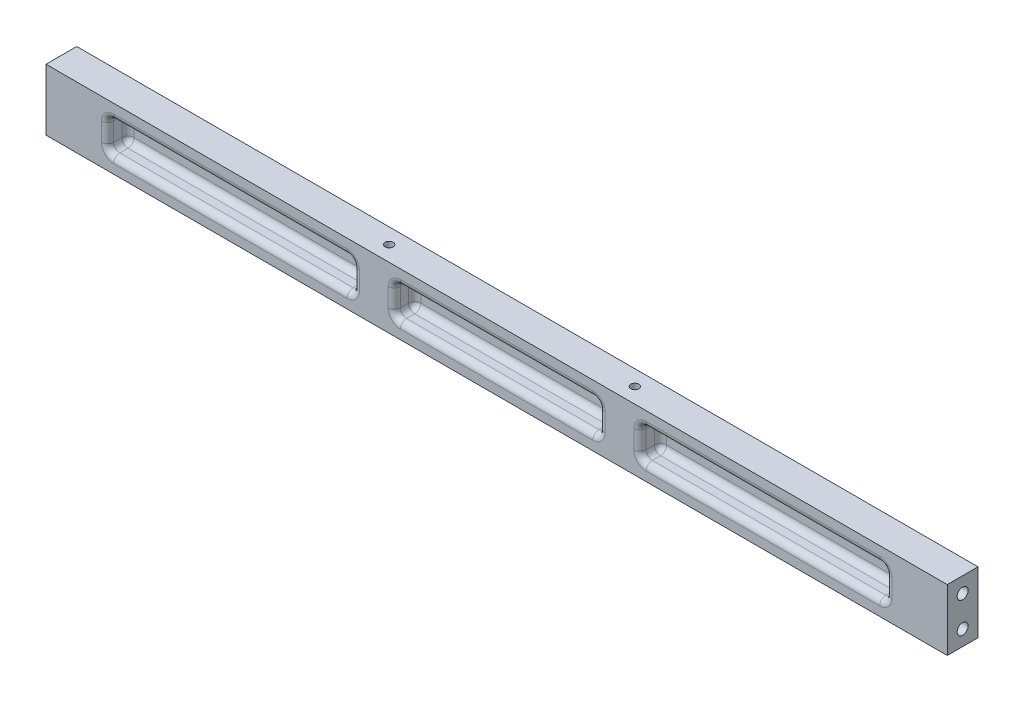
SolidWorks part; units mm, degrees
material "Alum 6061 (Default)"
ref_plane "Front Plane" through (0, 0, 0) normal (0, 0, 1) x (1, 0, 0)
ref_plane "Top Plane" through (0, 0, 0) normal (0, 1, 0) x (1, 0, 0)
ref_plane "Right Plane" through (0, 0, 0) normal (1, 0, 0) x (0, 0, -1)
sketch "Sketch1" plane through (0, 0, 0) normal (0, 0, 1) x (1, 0, 0)
  line L1 (-279.4, 19.05) -> (279.4, 19.05)
  line L2 (-279.4, 19.05) -> (-279.4, -19.05)
  line L3 (-279.4, -19.05) -> (279.4, -19.05)
  line L4 (279.4, 19.05) -> (279.4, -19.05)
  line L5 (-279.4, 19.05) -> (279.4, -19.05) construction
  line L6 (-279.4, -19.05) -> (279.4, 19.05) construction
  point P0 (0, 0)
  dimension "SpreadWidthT" = 558.8
  dimension "Height" = 38.1
extrude "Extrude1" add sketch "Sketch1" along normal mid plane 19.05
hole_wizard "M8x1.25 Tapped Hole1" positions "Sketch6" profile "Sketch7" tap size "M8x1.25" standard "ANSI Metric"
sketch "Sketch6" plane through (-279.4, 0, 0) normal (-1, 0, 0) x (0, 0, 1)
  line L0 (0, 9.525) -> (0, -9.525) construction
  point P0 (0, 9.525)
  point P2 (0, -9.525)
  point P10 (0, 0)
  dimension "D1" = 19.05
sketch "Sketch7" plane through (-279.4, 9.525, 0) normal (0, 1, 0) x (0, 0, 1)
  line L0 (0, 0) -> (0, 21.8549)
  line L1 (0, 21.8549) -> (3.4, 19.812)
  line L2 (3.4, 19.812) -> (3.4, 0)
  line L5 (3.4, 0) -> (0, 0)
  line L10 (0, 21.8549) -> (-3.4, 19.812) construction
  line L11 (0, -6.35) -> (0, 107.95) construction
  dimension "Tap Drill Dia." = 6.8
  dimension "Tap Drill Depth" = 19.812
  dimension "Drill Angle" = 118
cosmetic thread "Hole Thread1" parameters "D1"=16.002, "D2"=8
cosmetic thread "Hole Thread2" parameters "D1"=16.002, "D2"=8
hole_wizard "M8x1.25 Tapped Hole2" positions "Sketch8" profile "Sketch9" tap size "M8x1.25" standard "ANSI Metric"
sketch "Sketch8" plane through (279.4, 0, 0) normal (1, 0, 0) x (0, 0, -1)
  point P0 (0, 9.525)
  point P3 (0, -9.525)
sketch "Sketch9" plane through (279.4, 9.525, 0) normal (0, 1, 0) x (0, 0, -1)
  line L0 (0, 0) -> (0, 21.8549)
  line L1 (0, 21.8549) -> (3.4, 19.812)
  line L2 (3.4, 19.812) -> (3.4, 0)
  line L5 (3.4, 0) -> (0, 0)
  line L10 (0, 21.8549) -> (-3.4, 19.812) construction
  line L11 (0, -6.35) -> (0, 107.95) construction
  dimension "Tap Drill Dia." = 6.8
  dimension "Tap Drill Depth" = 19.812
  dimension "Drill Angle" = 118
cosmetic thread "Hole Thread3" parameters "D1"=16.002, "D2"=8
cosmetic thread "Hole Thread4" parameters "D1"=16.002, "D2"=8
hole_wizard "M6x1.0 Tapped Hole1" positions "Sketch10" profile "Sketch11" tap size "M6x1.0" standard "ANSI Metric"
sketch "Sketch10" plane through (0, 19.05, 0) normal (0, 1, 0) x (1, 0, 0)
  line L0 (-76.2, 0) -> (76.2, 0) construction
  point P15 (-76.2, 0)
  point P17 (76.2, 0)
  point P24 (0, 0)
  dimension "D1" = 152.4
sketch "Sketch11" plane through (-76.2, 19.05, 0) normal (1, 0, 0) x (0, 0, 1)
  line L0 (0, 0) -> (0, 14.2022)
  line L1 (0, 14.2022) -> (2.5, 12.7)
  line L2 (2.5, 12.7) -> (2.5, 0)
  line L5 (2.5, 0) -> (0, 0)
  line L10 (0, 14.2022) -> (-2.5, 12.7) construction
  line L11 (0, -6.35) -> (0, 107.95) construction
  dimension "Tap Drill Dia." = 5
  dimension "Tap Drill Depth" = 12.7
  dimension "Drill Angle" = 118
cosmetic thread "Hole Thread5" parameters "D1"=12.7, "D2"=6
cosmetic thread "Hole Thread6" parameters "D1"=12.7, "D2"=6
sketch "Sketch12" plane through (0, 0, 9.525) normal (0, 0, 1) x (1, 0, 0)
  line L0 (-279.4, 19.05) -> (-279.4, -19.05) construction
  line L13 (-63.5, 9.525) -> (63.5, 9.525)
  line L14 (-63.5, 9.525) -> (-63.5, -9.525)
  line L15 (-63.5, -9.525) -> (63.5, -9.525)
  line L16 (63.5, 9.525) -> (63.5, -9.525)
  line L17 (-63.5, 9.525) -> (63.5, -9.525) construction
  line L18 (-63.5, -9.525) -> (63.5, 9.525) construction
  line L19 (88.9, 9.525) -> (241.3, 9.525)
  line L20 (88.9, 9.525) -> (88.9, -9.525)
  line L21 (88.9, -9.525) -> (241.3, -9.525)
  line L22 (241.3, 9.525) -> (241.3, -9.525)
  line L23 (88.9, 9.525) -> (241.3, -9.525) construction
  line L24 (88.9, -9.525) -> (241.3, 9.525) construction
  line L25 (-241.3, 9.525) -> (-88.9, 9.525)
  line L26 (-241.3, 9.525) -> (-241.3, -9.525)
  line L27 (-241.3, -9.525) -> (-88.9, -9.525)
  line L28 (-88.9, 9.525) -> (-88.9, -9.525)
  line L29 (-241.3, 9.525) -> (-88.9, -9.525) construction
  line L30 (-241.3, -9.525) -> (-88.9, 9.525) construction
  point P0 (0, 0)
  point P5 (165.1, 0)
  point P10 (-165.1, 0)
  dimension "D1" = 19.05
  dimension "D2" = 25.4
  dimension "D3" = 38.1
  dimension "D4" = 127
  dimension "D5" = 25.4
extrude "Cut-Extrude1" cut sketch "Sketch12" against normal blind 12.7
fillet "Fillet1" radius 3.81 35 edges at (241.3, 0, 9.525) (-88.9, 0, 9.525) (-241.3, 0, 9.525) (241.3, 9.525, 3.175) (165.1, 9.525, -3.175) (165.1, 9.525, 9.525) (88.9, 0, -3.175) (88.9, 0, 9.525) (165.1, -9.525, -3.175) (241.3, -9.525, 3.175) (165.1, -9.525, 9.525) (0, -9.525, -3.175) (0, -9.525, 9.525) (0, 9.525, -3.175) (0, 9.525, 9.525) (63.5, 0, -3.175) (63.5, 0, 9.525) (-63.5, 0, -3.175) (-63.5, 0, 9.525) (-165.1, -9.525, 9.525) (-165.1, 9.525, 9.525) (-165.1, -9.525, -3.175) (-241.3, 0, -3.175) (-165.1, 9.525, -3.175) (-88.9, 0, -3.175) (88.9, 9.525, 3.175) (88.9, -9.525, 3.175) (63.5, -9.525, 3.175) (63.5, 9.525, 3.175) (-63.5, 9.525, 3.175) (-63.5, -9.525, 3.175) (-241.3, -9.525, 3.175) (-88.9, -9.525, 3.175) (-88.9, 9.525, 3.175) (-241.3, 9.525, 3.175)
